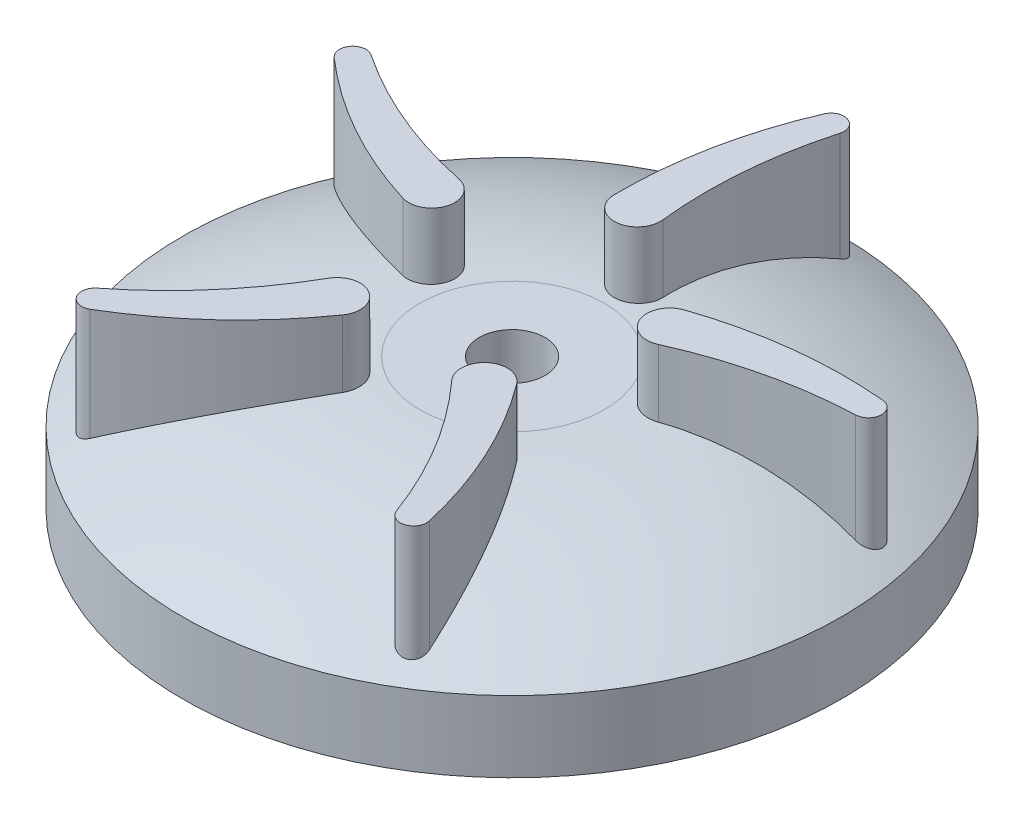
SolidWorks part; units mm, degrees
ref_plane "Přední rovina" through (0, 0, 0) normal (0, 0, 1) x (1, 0, 0)
ref_plane "Vrchní rovina" through (0, 0, 0) normal (0, 1, 0) x (1, 0, 0)
ref_plane "Pravá rovina" through (0, 0, 0) normal (1, 0, 0) x (0, 0, -1)
sketch "Skica1" plane through (0, 0, 0) normal (0, 0, 1) x (1, 0, 0)
  line L0 (0, 0) -> (0, 20)
  line L1 (0, 20) -> (14, 20)
  line L2 (50, 10.7951) -> (50, 0)
  line L3 (50, 0) -> (0, 0)
  arc A0 (14, 20) -> (50, 10.7951) centre (14, -55) cw
  dimension "RC" = 75
  dimension "RA" = 50
  dimension "H1" = 20
  dimension "RB" = 14
revolve "Rotovat1" add sketch "Skica1" angle 360 about L0
sketch "Skica2" plane through (0, 20, 0) normal (0, 1, 0) x (1, 0, 0)
  circle A0 centre (0, 0) radius 5
  dimension "D1" = 10
extrude "Odebrat vysunutím1" cut sketch "Skica2" against normal up to next
sketch "Skica3" plane through (0, 20, 0) normal (0, 1, 0) x (1, 0, 0)
  line L0 (-0.9372, 12.3316) -> (3.5664, 44.3762) construction
  line L1 (0, 0) -> (0, 61.3609) construction
  arc A0 (5.5429, 44.2025) -> (1.7812, 45.5371) centre (3.6185, 44.747) ccw
  arc A1 (3.4789, 19.3835) -> (-3.4997, 18.9511) centre (0, 19) cw
  arc A2 (1.7812, 45.5371) -> (-3.4997, 18.9511) centre (61.494, 19.8587) ccw
  arc A3 (5.5429, 44.2025) -> (3.4789, 19.3835) centre (68.0875, 26.5057) ccw
  point P4 (0, 0)
  point P7 (5.9799, 19)
  point P14 (0, 0)
  dimension "D1" = 65
  dimension "D2" = 2
  dimension "D3" = 3.5
  dimension "D4" = 26
  dimension "D5" = 19
  dimension "D6" = 8
extrude "Přidat vysunutím1" add sketch "Skica3" along normal blind 10 and the other way up to next contours A2 A1 A3 A0
pattern_circular "Kruhové pole1" count 5 over 360 about axis through (0, 0, 0) along (0, 1, 0) of "Přidat vysunutím1"
